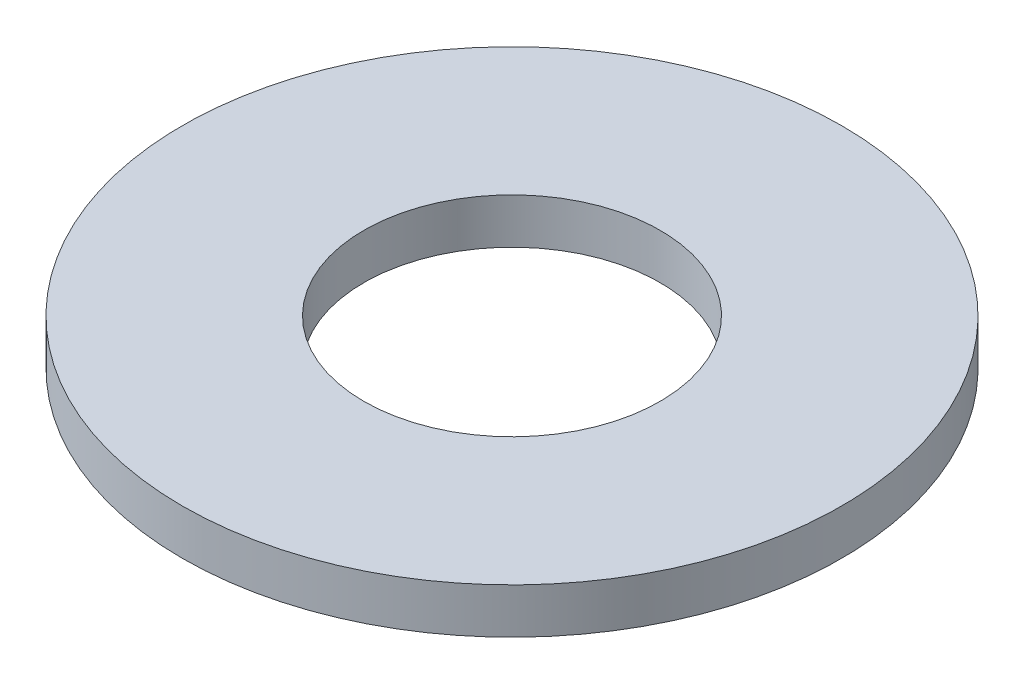
SolidWorks part; units mm, degrees
material "Plain Carbon Steel"
ref_plane "Front Plane" through (0, 0, 0) normal (0, 0, 1) x (1, 0, 0)
ref_plane "Top Plane" through (0, 0, 0) normal (0, 1, 0) x (1, 0, 0)
ref_plane "Right Plane" through (0, 0, 0) normal (1, 0, 0) x (0, 0, -1)
sketch "Sketch1" plane through (0, 0, 0) normal (0, 1, 0) x (1, 0, 0)
  circle A0 centre (0, 0) radius 7.9375
  dimension "OD" = 15.875
extrude "Boss-Extrude1" add sketch "Sketch1" along normal blind 1.0922
sketch "Sketch5" plane through (0, 1.0922, 0) normal (0, 1, 0) x (-1, 0, 0)
  circle A0 centre (0, 0) radius 3.5687
  dimension "ID" = 7.1374
extrude "Cut-Extrude1" cut sketch "Sketch5" against normal through all
